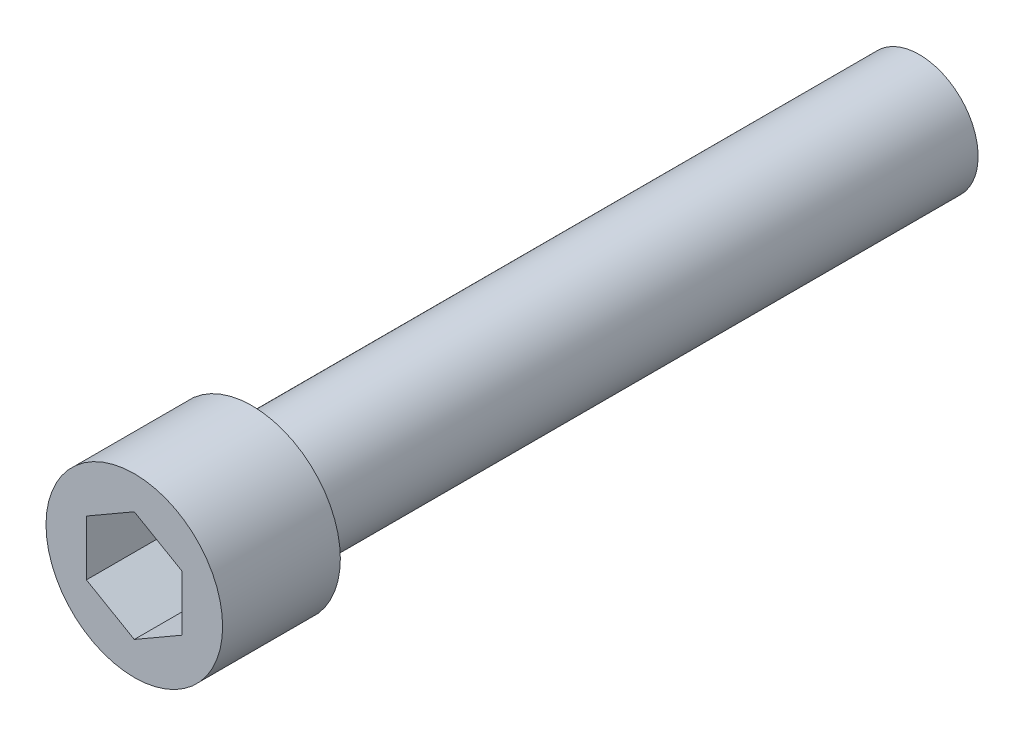
SolidWorks part; units mm, degrees
material "AISI 4130 Steel, normalized at 870C"
ref_plane "Front Plane" through (0, 0, 0) normal (0, 0, 1) x (1, 0, 0)
ref_plane "Top Plane" through (0, 0, 0) normal (0, 1, 0) x (1, 0, 0)
ref_plane "Right Plane" through (0, 0, 0) normal (1, 0, 0) x (0, 0, -1)
sketch "Sketch1" plane through (0, 0, 0) normal (0, 0, 1) x (1, 0, 0)
  line L1 (0, 2.8177) -> (-2.4402, 1.4089)
  line L2 (-2.4402, 1.4089) -> (-2.4402, -1.4089)
  line L3 (-2.4402, -1.4089) -> (0, -2.8177)
  line L4 (0, -2.8177) -> (2.4402, -1.4089)
  line L5 (2.4402, -1.4089) -> (2.4402, 1.4089)
  line L6 (2.4402, 1.4089) -> (0, 2.8177)
  circle A0 centre (0, 0) radius 4.5
  circle A1 centre (0, 0) radius 2.4402 construction
extrude "Boss-Extrude1" add sketch "Sketch1" along normal blind 4
sketch "Sketch2" plane through (0, 0, 0) normal (0, 0, -1) x (-1, 0, 0)
  circle A0 centre (0, 0) radius 4.5
extrude "Boss-Extrude2" add sketch "Sketch2" along normal blind 2
sketch "Sketch3" plane through (0, 0, -2) normal (0, 0, -1) x (-1, 0, 0)
  circle A0 centre (0, 0) radius 3
extrude "Boss-Extrude3" add sketch "Sketch3" along normal blind 34
